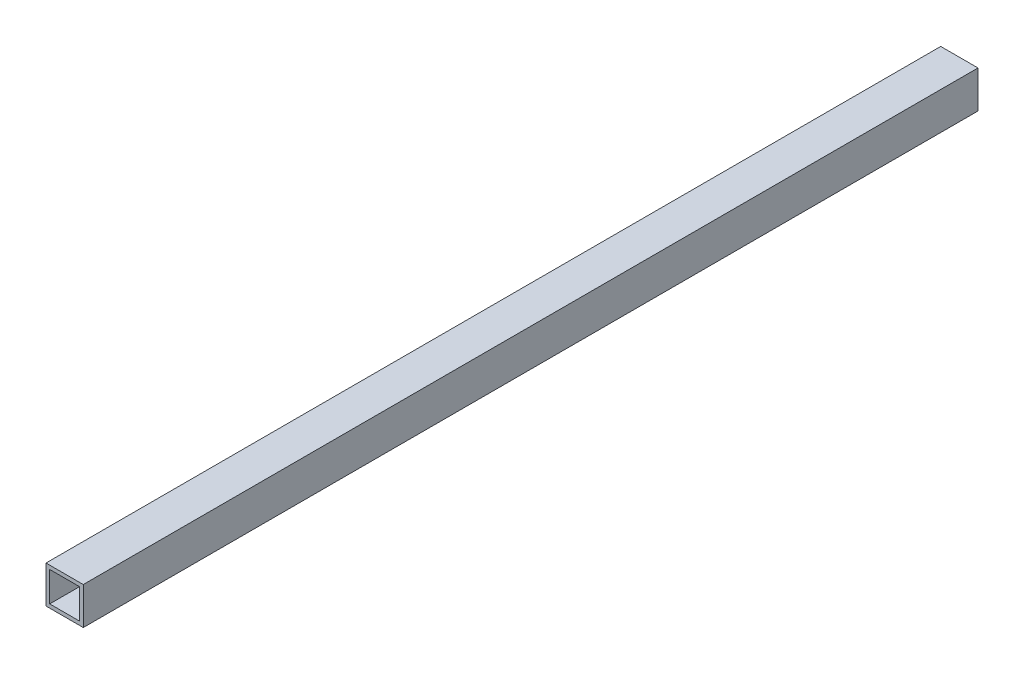
SolidWorks part; units mm, degrees
material "1.0037 (S235JR)"
ref_plane "Front Plane" through (0, 0, 0) normal (0, 0, 1) x (1, 0, 0)
ref_plane "Top Plane" through (0, 0, 0) normal (0, 1, 0) x (1, 0, 0)
ref_plane "Right Plane" through (0, 0, 0) normal (1, 0, 0) x (0, 0, -1)
curve "Curve1"
  spline degree 1 poles (0, 0, -460) (0, 0, 500) knots 0 0 1 1
sketch "Sketch1" plane through (0, 0, 0) normal (0, 0, 1) x (1, 0, 0)
  line L0 (0, 35.3535) -> (0, -33.8384) construction
  line L1 (-20, 20) -> (20, 20)
  line L2 (-20, 20) -> (-20, -20)
  line L3 (-20, -20) -> (20, -20)
  line L4 (20, 20) -> (20, -20)
  line L5 (-16, 16) -> (16, 16)
  line L6 (-16, 16) -> (-16, -16)
  line L7 (-16, -16) -> (16, -16)
  line L8 (16, 16) -> (16, -16)
  line L9 (-39.3939, 0) -> (41.5152, 0) construction
  dimension "D1" = 40
  dimension "D2" = 32
sweep "Sweep1" add profiles "Sketch1" path "Curve1"
